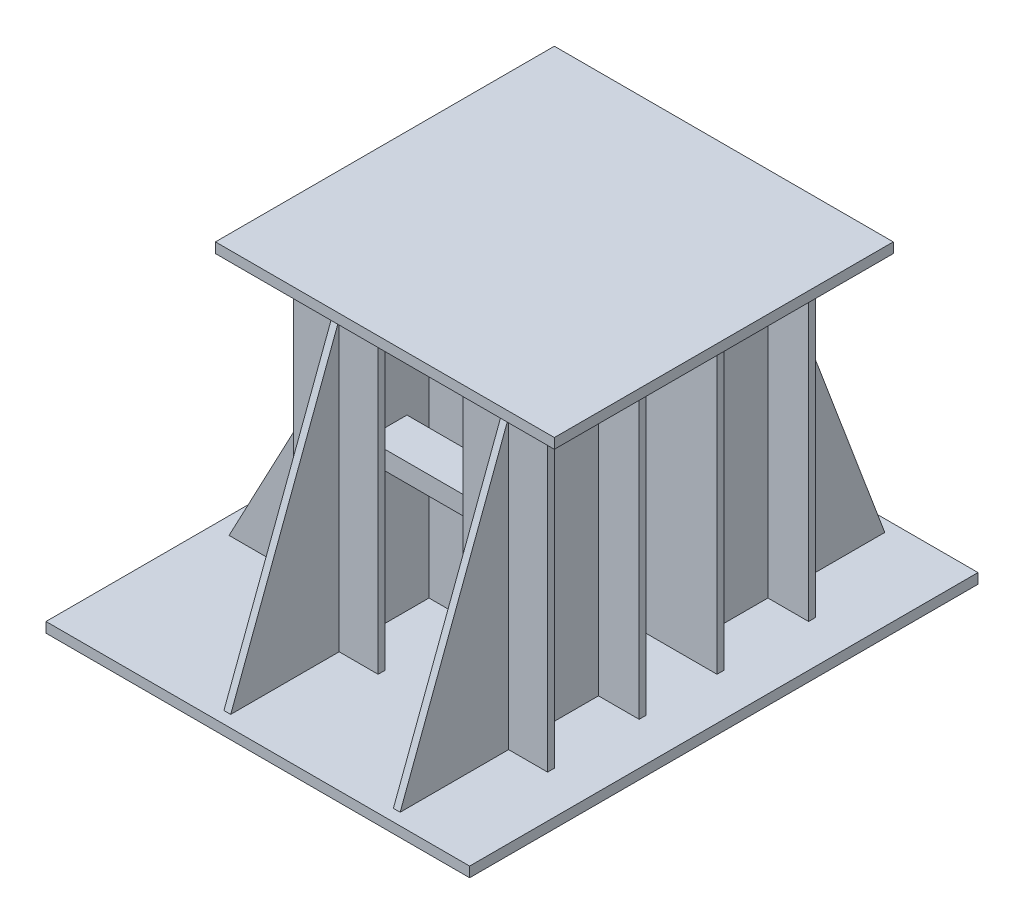
SolidWorks part; units mm, degrees
ref_plane "Front Plane" through (0, 0, 0) normal (0, 0, 1) x (1, 0, 0)
ref_plane "Top Plane" through (0, 0, 0) normal (0, 1, 0) x (1, 0, 0)
ref_plane "Right Plane" through (0, 0, 0) normal (1, 0, 0) x (0, 0, -1)
sketch "Sketch5" plane through (0, 0, 0) normal (0, 1, 0) x (1, 0, 0)
  line L0 (-769.2308, -230.8501) -> (-769.2308, -1230.8501)
  line L1 (-769.2308, -1230.8501) -> (230.7692, -1230.8501)
  line L2 (230.7692, -1230.8501) -> (230.7692, -230.8501)
  line L3 (230.7692, -230.8501) -> (-769.2308, -230.8501)
  dimension "D1" = 1000
  dimension "D2" = 1000
extrude "Boss-Extrude1" add sketch "Sketch5" along normal blind 30
sketch "Sketch6" plane through (0, 0, 0) normal (0, -1, 0) x (1, 0, 0)
  line L0 (-644.2308, 625.8501) -> (-644.2308, 605.8501)
  line L1 (-644.2308, 605.8501) -> (-524.0884, 605.8501)
  line L2 (-524.0884, 605.8501) -> (-524.0884, 355.8501)
  line L3 (-524.0884, 355.8501) -> (-644.0884, 355.8501)
  line L4 (-644.0884, 355.8501) -> (-644.0884, 335.8501)
  line L5 (-644.0884, 335.8501) -> (-394.0884, 335.8501)
  line L6 (-394.0884, 335.8501) -> (-394.0884, 355.8501)
  line L7 (-394.0884, 355.8501) -> (-514.0884, 355.8501)
  line L8 (-514.0884, 355.8501) -> (-514.0884, 605.8501)
  line L9 (-514.0884, 605.8501) -> (-394.2308, 605.8501)
  line L10 (-394.2308, 605.8501) -> (-394.2308, 625.8501)
  line L11 (-394.2308, 625.8501) -> (-644.2308, 625.8501)
  line L12 (-769.2308, 230.8501) -> (-769.2308, 1230.8501) construction
  line L13 (230.7692, 230.8501) -> (-769.2308, 230.8501) construction
  line L14 (-644.2308, 1125.8501) -> (-644.2308, 1105.8501)
  line L15 (-644.2308, 1105.8501) -> (-524.0884, 1105.8501)
  line L16 (-524.0884, 1105.8501) -> (-524.0884, 855.8501)
  line L17 (-524.0884, 855.8501) -> (-644.0884, 855.8501)
  line L18 (-644.0884, 855.8501) -> (-644.0884, 835.8501)
  line L19 (-644.0884, 835.8501) -> (-394.0884, 835.8501)
  line L20 (-394.0884, 835.8501) -> (-394.0884, 855.8501)
  line L21 (-394.0884, 855.8501) -> (-514.0884, 855.8501)
  line L22 (-514.0884, 855.8501) -> (-514.0884, 1105.8501)
  line L23 (-514.0884, 1105.8501) -> (-394.2308, 1105.8501)
  line L24 (-394.2308, 1105.8501) -> (-394.2308, 1125.8501)
  line L25 (-394.2308, 1125.8501) -> (-644.2308, 1125.8501)
  line L26 (-144.2308, 1125.8501) -> (-144.2308, 1105.8501)
  line L27 (-144.2308, 1105.8501) -> (-24.0884, 1105.8501)
  line L28 (-24.0884, 1105.8501) -> (-24.0884, 855.8501)
  line L29 (-24.0884, 855.8501) -> (-144.0884, 855.8501)
  line L30 (-144.0884, 855.8501) -> (-144.0884, 835.8501)
  line L31 (-144.0884, 835.8501) -> (105.9116, 835.8501)
  line L32 (105.9116, 835.8501) -> (105.9116, 855.8501)
  line L33 (105.9116, 855.8501) -> (-14.0884, 855.8501)
  line L34 (-14.0884, 855.8501) -> (-14.0884, 1105.8501)
  line L35 (-14.0884, 1105.8501) -> (105.7692, 1105.8501)
  line L36 (105.7692, 1105.8501) -> (105.7692, 1125.8501)
  line L37 (105.7692, 1125.8501) -> (-144.2308, 1125.8501)
  line L38 (-144.2308, 625.8501) -> (-144.2308, 605.8501)
  line L39 (-144.2308, 605.8501) -> (-24.0884, 605.8501)
  line L40 (-24.0884, 605.8501) -> (-24.0884, 355.8501)
  line L41 (-24.0884, 355.8501) -> (-144.0884, 355.8501)
  line L42 (-144.0884, 355.8501) -> (-144.0884, 335.8501)
  line L43 (-144.0884, 335.8501) -> (105.9116, 335.8501)
  line L44 (105.9116, 335.8501) -> (105.9116, 355.8501)
  line L45 (105.9116, 355.8501) -> (-14.0884, 355.8501)
  line L46 (-14.0884, 355.8501) -> (-14.0884, 605.8501)
  line L47 (-14.0884, 605.8501) -> (105.7692, 605.8501)
  line L48 (105.7692, 605.8501) -> (105.7692, 625.8501)
  line L49 (105.7692, 625.8501) -> (-144.2308, 625.8501)
  line L50 (230.7692, 1230.8501) -> (230.7692, 230.8501) construction
  line L51 (-769.2308, 1230.8501) -> (230.7692, 1230.8501) construction
  point P9 (-519.2308, 625.8501)
  point P15 (-524.0884, 480.8501)
  point P27 (-519.2308, 1125.8501)
  point P31 (0, 0)
  point P41 (-19.2308, 1125.8501)
  point P45 (-24.0884, 980.8501)
  point P55 (-19.2308, 625.8501)
  point P59 (0, 0)
  point P62 (-514.0884, 980.8501)
  point P65 (-14.0884, 480.8501)
  dimension "D1" = 250
  dimension "D2" = 250
  dimension "D3" = 250
  dimension "D4" = 250
  dimension "D5" = 10
  dimension "D6" = 120
  dimension "D7" = 120
  dimension "D8" = 20
  dimension "D9" = 20
  dimension "D10" = 250
  dimension "D11" = 250
  dimension "D12" = 250
  dimension "D13" = 250
  dimension "D14" = 250
  dimension "D15" = 120
  dimension "D16" = 120
  dimension "D17" = 20
  dimension "D18" = 20
  dimension "D19" = 250
  dimension "D20" = 250
  dimension "D21" = 250
  dimension "D22" = 120
  dimension "D23" = 120
  dimension "D24" = 20
  dimension "D25" = 20
  dimension "D26" = 250
  dimension "D27" = 250
  dimension "D28" = 250
  dimension "D29" = 120
  dimension "D30" = 120
  dimension "D31" = 20
  dimension "D32" = 20
  dimension "D33" = 250
  dimension "D34" = 250
  dimension "D35" = 250
  dimension "D36" = 250
  dimension "D37" = 250
  dimension "D38" = 250
extrude "Boss-Extrude2" add sketch "Sketch6" along normal blind 940 contours L22 L23 L24 L25 L14 L15 L16 L17 L18 L19 L20 L21 | L34 L35 L36 L37 L26 L27 L28 L29 L30 L31 L32 L33 | L2 L3 L4 L5 L6 L7 L8 L9 L10 L11 L0 L1 | L47 L48 L49 L38 L39 L40 L41 L42 L43 L44 L45 L46
sketch "Sketch7" plane through (0, -940, 0) normal (0, -1, 0) x (1, 0, 0)
  line L0 (-1019.2308, 1480.8501) -> (-1019.2308, -19.1499)
  line L1 (-1019.2308, -19.1499) -> (230.7692, -19.1499)
  line L2 (230.7692, -19.1499) -> (230.7692, 1480.8501)
  line L3 (230.7692, 1480.8501) -> (-1019.2308, 1480.8501)
  line L4 (-769.2308, 1230.8501) -> (230.7692, 1230.8501) construction
  line L5 (230.7692, 230.8501) -> (-769.2308, 230.8501) construction
  line L6 (230.7692, 1230.8501) -> (230.7692, 230.8501) construction
  dimension "D1" = 1250
  dimension "D2" = 1500
  dimension "D3" = 250
  dimension "D4" = 250
extrude "Boss-Extrude3" add sketch "Sketch7" along normal blind 30
sketch "Sketch8" plane through (-524.0884, 0, 0) normal (-1, 0, 0) x (0, 0, 1)
  line L0 (480.8501, -100) -> (470.8501, -100)
  line L1 (470.8501, -100) -> (470.8501, -940)
  line L2 (605.8501, -940) -> (355.8501, -940) construction
  line L3 (470.8501, -940) -> (490.8501, -940)
  line L4 (1480.8501, -940) -> (-19.1499, -940) construction
  line L5 (490.8501, -940) -> (490.8501, -100)
  line L6 (490.8501, -100) -> (480.8501, -100)
  line L7 (605.8501, -940) -> (605.8501, 0) construction
  line L8 (355.8501, -940) -> (355.8501, 0) construction
  line L9 (975.8501, -100) -> (970.8501, -100)
  line L10 (970.8501, -100) -> (970.8501, -940)
  line L11 (970.8501, -940) -> (990.8501, -940)
  line L12 (990.8501, -940) -> (990.8501, -100)
  line L13 (990.8501, -100) -> (975.8501, -100)
  line L14 (1105.8501, -940) -> (855.8501, -940) construction
  line L15 (855.8501, -940) -> (855.8501, 0) construction
  line L16 (1105.8501, -940) -> (1105.8501, 0) construction
  point P2 (0, 0)
  point P10 (0, 0)
  point P26 (0, 0)
  dimension "D1" = 10
  dimension "D2" = 10
  dimension "D3" = 115
  dimension "D4" = 115
  dimension "D5" = 840
  dimension "D6" = 115
  dimension "D7" = 115
  dimension "D8" = 20
  dimension "D9" = 840
extrude "Boss-Extrude4" add sketch "Sketch8" along normal blind 445
sketch "Sketch10" plane through (0, 0, 470.8501) normal (0, 0, -1) x (-1, 0, 0)
  line L0 (524.0884, -100) -> (969.0884, -940)
  line L1 (969.0884, -940) -> (969.0884, -100)
  line L2 (969.0884, -100) -> (524.0884, -100)
extrude "Cut-Extrude2" cut sketch "Sketch10" against normal blind 30
sketch "Sketch11" plane through (0, 0, 990.8501) normal (0, 0, 1) x (1, 0, 0)
  line L0 (-969.0884, -100) -> (-524.0884, -100)
  line L1 (-524.0884, -100) -> (-969.0884, -940)
  line L2 (-969.0884, -940) -> (-969.0884, -100)
extrude "Cut-Extrude3" cut sketch "Sketch11" against normal blind 30
sketch "Sketch12" plane through (0, 0, 1125.8501) normal (0, 0, 1) x (1, 0, 0)
  line L0 (-529.2308, -940) -> (-509.2308, -940)
  line L1 (230.7692, -940) -> (-1019.2308, -940) construction
  line L2 (-509.2308, -940) -> (-509.2308, -90)
  line L3 (-509.2308, -90) -> (-529.2308, -90)
  line L4 (-529.2308, -90) -> (-529.2308, -940)
  line L5 (-394.2308, -940) -> (-394.2308, 0) construction
  line L6 (-644.2308, -940) -> (-644.2308, 0) construction
  line L7 (-29.2308, -940) -> (-9.2308, -940)
  line L8 (-9.2308, -940) -> (-9.2308, -90)
  line L9 (-9.2308, -90) -> (-29.2308, -90)
  line L10 (-29.2308, -90) -> (-29.2308, -940)
  line L11 (105.7692, -940) -> (-144.2308, -940) construction
  line L12 (-144.2308, -940) -> (-144.2308, 0) construction
  line L13 (105.7692, -940) -> (105.7692, 0) construction
  point P8 (-394.2308, -470)
  point P21 (0, 0)
  dimension "D1" = 20
  dimension "D2" = 850
  dimension "D3" = 115
  dimension "D4" = 115
  dimension "D5" = 850
  dimension "D6" = 20
  dimension "D7" = 115
  dimension "D8" = 115
extrude "Boss-Extrude5" add sketch "Sketch12" along normal blind 320 contours L2 L3 L4 L0 | L10 L7 L8 L9
sketch "Sketch13" plane through (-529.2308, 0, 0) normal (-1, 0, 0) x (0, 0, 1)
  line L0 (1125.8501, -90) -> (1445.8501, -940)
  line L1 (1445.8501, -940) -> (1445.8501, -90)
  line L2 (1445.8501, -90) -> (1125.8501, -90)
extrude "Cut-Extrude4" cut sketch "Sketch13" against normal blind 700
sketch "Sketch14" plane through (0, -940, 0) normal (0, 1, 0) x (1, 0, 0)
  line L0 (-1613.3236, -730.8501) -> (-1613.3236, -310.3688) construction
  line L2 (-1613.3236, -730.8501) -> (381.6548, -730.8501) construction
  line L3 (-1613.3236, -310.3688) -> (381.6548, -310.3688) construction
  line L4 (381.6548, -310.3688) -> (381.6548, -730.8501) construction
ref_plane "Plane1" through (0, 0, 730.8501) normal (0, 0, -1) x (-1, 0, 0)
mirror "Mirror1" about plane through (0, 0, 730.8501) normal (0, 0, -1) of "Boss-Extrude5"
mirror "Mirror2" about plane through (0, 0, 730.8501) normal (0, 0, -1) of "Cut-Extrude4"
sketch "Sketch15" plane through (0, 0, 835.8501) normal (0, 0, -1) x (-1, 0, 0)
  line L0 (549.0884, -495) -> (579.0884, -495)
  line L1 (579.0884, -495) -> (579.0884, -440)
  line L2 (579.0884, -440) -> (459.0884, -440)
  line L3 (459.0884, -440) -> (459.0884, -495)
  line L4 (459.0884, -495) -> (489.0884, -495)
  line L5 (489.0884, -495) -> (489.0884, -470)
  line L6 (489.0884, -470) -> (549.0884, -470)
  line L7 (549.0884, -470) -> (549.0884, -495)
  line L8 (644.0884, -940) -> (394.0884, -940) construction
  line L9 (644.0884, -940) -> (644.0884, 0) construction
  line L10 (394.0884, -940) -> (394.0884, 0) construction
  dimension "D1" = 120
  dimension "D2" = 30
  dimension "D3" = 30
  dimension "D4" = 60
  dimension "D5" = 55
  dimension "D6" = 55
  dimension "D7" = 25
  dimension "D8" = 30
  dimension "D9" = 445
  dimension "D10" = 65
  dimension "D11" = 65
extrude "Boss-Extrude6" add sketch "Sketch15" along normal up to surface (210 mm away) up to face at (-519.2308, -470, 625.8501)
sketch "Sketch18" plane through (-514.0884, 0, 0) normal (1, 0, 0) x (0, 0, -1)
  line L0 (-950.8501, -495) -> (-920.8501, -495)
  line L1 (-920.8501, -495) -> (-920.8501, -440)
  line L2 (-920.8501, -440) -> (-1040.8501, -440)
  line L3 (-1040.8501, -440) -> (-1040.8501, -495)
  line L4 (-1040.8501, -495) -> (-1010.8501, -495)
  line L5 (-1010.8501, -495) -> (-1010.8501, -470)
  line L6 (-1010.8501, -470) -> (-950.8501, -470)
  line L7 (-950.8501, -470) -> (-950.8501, -495)
  line L8 (-855.8501, -940) -> (-1105.8501, -940) construction
  line L9 (-1105.8501, -940) -> (-1105.8501, 0) construction
  line L10 (-855.8501, -940) -> (-855.8501, 0) construction
  dimension "D1" = 445
  dimension "D2" = 120
  dimension "D3" = 65
  dimension "D4" = 65
  dimension "D5" = 30
  dimension "D6" = 30
  dimension "D7" = 55
  dimension "D8" = 25
  dimension "D9" = 30
extrude "Boss-Extrude7" add sketch "Sketch18" along normal up to surface (490 mm away) up to face at (-24.0884, -470, 980.8501)
mirror "Mirror3" about plane through (0, 0, 730.8501) normal (0, 0, -1) of "Boss-Extrude7"
